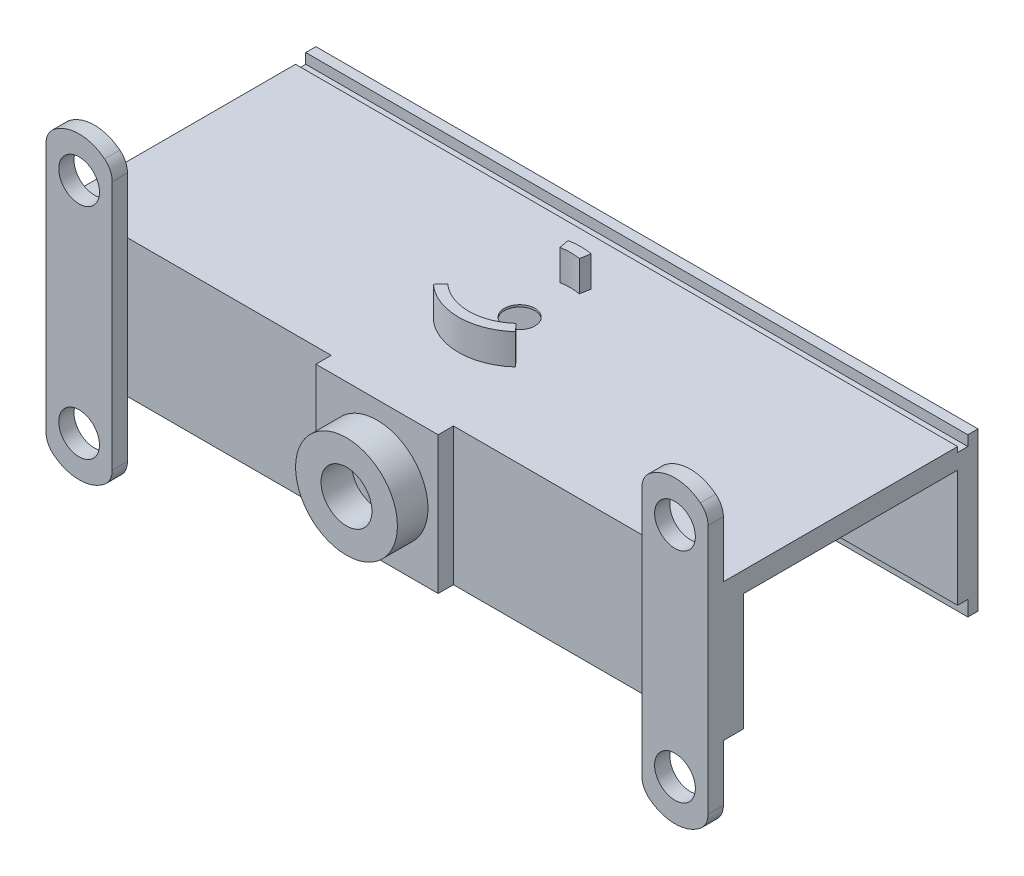
SolidWorks part; units mm, degrees
ref_plane "Alzado" through (0, 0, 0) normal (0, 0, 1) x (1, 0, 0)
ref_plane "Planta" through (0, 0, 0) normal (0, 1, 0) x (1, 0, 0)
ref_plane "Vista lateral" through (0, 0, 0) normal (1, 0, 0) x (0, 0, -1)
sketch "Croquis1" plane through (0, 0, 0) normal (0, 1, 0) x (1, 0, 0)
  line L0 (-32.5, 0) -> (32.5, 0)
  line L1 (32.5, 0) -> (32.5, -25)
  line L2 (32.5, -25) -> (-32.5, -25)
  line L3 (-32.5, -25) -> (-32.5, 0)
  dimension "D1" = 25
  dimension "D2" = 65
extrude "Saliente-Extruir4" add sketch "Croquis1" along normal blind 13.5
sketch "Croquis5" plane through (0, 0, 25) normal (0, 0, 1) x (1, 0, 0)
  line L0 (32.5, 0) -> (32.5, -5.5184)
  line L1 (-32.5, 13.5) -> (32.5, 13.5) construction
  line L2 (26, 13.5) -> (26, 0)
  line L3 (-32.5, 0) -> (32.5, 0) construction
  line L4 (26, 0) -> (26, -5.5184)
  line L5 (32.5, 0) -> (32.5, 13.5)
  line L6 (-32.5, 0) -> (-32.5, -5.5184)
  line L7 (26, 13.5) -> (26, 19.0184)
  line L8 (32.5, 13.5) -> (32.5, 19.0184)
  line L9 (-32.5, 6.75) -> (32.5, 6.75) construction
  line L10 (-32.5, 13.5) -> (-32.5, 0) construction
  line L11 (0, 19.3867) -> (0, -8.9745) construction
  line L12 (-26, 0) -> (-26, -5.5184)
  line L13 (-26, 13.5) -> (-26, 19.0184)
  line L14 (-32.5, 13.5) -> (-32.5, 19.0184)
  line L15 (-32.5, 0) -> (-32.5, 13.5)
  line L16 (-26, 13.5) -> (-26, 0)
  circle A0 centre (29.25, 17.4572) radius 2
  arc A1 (32.5, 19.0184) -> (31.75, 20.5797) centre (30.5, 19.0184) ccw
  arc A2 (26.75, 20.5797) -> (26, 19.0184) centre (28, 19.0184) ccw
  arc A3 (31.75, 20.5797) -> (26.75, 20.5797) centre (29.25, 17.4572) ccw
  arc A4 (32.5, -5.5184) -> (31.75, -7.0797) centre (30.5, -5.5184) cw
  arc A5 (31.75, -7.0797) -> (26.75, -7.0797) centre (29.25, -3.9572) cw
  arc A6 (26.75, -7.0797) -> (26, -5.5184) centre (28, -5.5184) cw
  circle A7 centre (29.25, -3.9572) radius 2
  arc A8 (-32.5, -5.5184) -> (-31.75, -7.0797) centre (-30.5, -5.5184) ccw
  arc A9 (-31.75, -7.0797) -> (-26.75, -7.0797) centre (-29.25, -3.9572) ccw
  arc A10 (-26.75, -7.0797) -> (-26, -5.5184) centre (-28, -5.5184) ccw
  arc A11 (-26.75, 20.5797) -> (-26, 19.0184) centre (-28, 19.0184) cw
  arc A12 (-31.75, 20.5797) -> (-26.75, 20.5797) centre (-29.25, 17.4572) cw
  arc A13 (-32.5, 19.0184) -> (-31.75, 20.5797) centre (-30.5, 19.0184) cw
  dimension "D2" = 4
  dimension "D3" = 2
  dimension "D1" = 6.5
sketch "Croquis6" plane through (32.5, 0, 0) normal (1, 0, 0) x (0, 0, -1)
  line L0 (-23, 0) -> (-23, 11.5)
  line L1 (-25, 0) -> (0, 0) construction
  line L2 (-23, 11.5) -> (-2, 11.5)
  line L3 (-2, 11.5) -> (-2, 0)
  line L4 (-2, 0) -> (-23, 0)
  line L5 (-25, 0) -> (-25, 13.5) construction
  line L6 (0, 13.5) -> (0, 0) construction
  line L7 (-25, 13.5) -> (0, 13.5) construction
  dimension "D1" = 2
  dimension "D2" = 2
  dimension "D3" = 2
extrude "Cortar-Extruir2" cut sketch "Croquis6" against normal blind 65
extrude "Saliente-Extruir6" add sketch "Croquis5" along normal blind 1.5
sketch "Croquis7" plane through (0, 0, 25) normal (0, 0, 1) x (1, 0, 0)
  line L0 (-26, -5.5184) -> (-26, 19.0184) construction
  line L1 (-26, 13.5) -> (26, 13.5) construction
  line L2 (-6, 13.5) -> (-6, 0)
  line L3 (-26, 0) -> (26, 0) construction
  line L4 (26, 13.5) -> (26, 0) construction
  line L5 (-6, 13.5) -> (6, 13.5)
  line L6 (6, 13.5) -> (6, 0)
  line L7 (-6, 0) -> (6, 0)
  dimension "D1" = 20
  dimension "D2" = 20
extrude "Saliente-Extruir7" add sketch "Croquis7" along normal blind 1.5
sketch "Croquis8" plane through (0, 0, 26.5) normal (0, 0, 1) x (1, 0, 0)
  line L0 (-6, 13.5) -> (6, 0) construction
  line L1 (-6, 0) -> (6, 13.5) construction
  circle A0 centre (0, 6.75) radius 5
  dimension "D1" = 10
extrude "Saliente-Extruir8" add sketch "Croquis8" along normal blind 3
sketch "Croquis9" plane through (0, 0, 29.5) normal (0, 0, 1) x (1, 0, 0)
  circle A0 centre (0, 6.75) radius 2.5
  dimension "D1" = 5
extrude "Cortar-Extruir3" cut sketch "Croquis9" against normal blind 3
sketch "Croquis10" plane through (0, 0, 0) normal (0, -1, 0) x (1, 0, 0)
  line L1 (-3, 25) -> (-3, 23)
  line L2 (-32.5, 23) -> (32.5, 23) construction
  line L3 (-3, 23) -> (3, 23)
  line L4 (3, 23) -> (3, 25)
  line L6 (-3, 25) -> (3, 25)
extrude "Cortar-Extruir4" cut sketch "Croquis10" against normal blind 10
sketch "Croquis11" plane through (0, 0, 26.5) normal (0, 0, 1) x (1, 0, 0)
  circle A0 centre (0, 6.75) radius 1.5
  dimension "D1" = 3
extrude "Cortar-Extruir5" cut sketch "Croquis11" against normal blind 10
sketch "Croquis12" plane through (0, 0, 26.5) normal (0, 0, 1) x (1, 0, 0)
  line L0 (-32.5, 6.75) -> (-26, 6.75) construction
  line L3 (-32.5, 19.0184) -> (-32.5, -5.5184) construction
  line L4 (-26, -5.5184) -> (-26, 19.0184) construction
  circle A0 centre (-29.25, 17.5) radius 2
  circle A1 centre (-29.25, -4) radius 2
  dimension "D2" = 4
extrude "Cortar-Extruir6" cut sketch "Croquis12" against normal blind 10
sketch "Croquis14" plane through (0, 0, 23) normal (0, 0, -1) x (-1, 0, 0)
  line L0 (-3, 10) -> (-3, 10.5)
  line L1 (32.5, 11.5) -> (-32.5, 11.5) construction
  line L2 (-2, 11.5) -> (2, 11.5)
  line L3 (3, 10.5) -> (3, 10)
  line L4 (3, 10) -> (-3, 10)
  arc A0 (-3, 10.5) -> (-2, 11.5) centre (-2, 10.5) cw
  arc A1 (2, 11.5) -> (3, 10.5) centre (2, 10.5) cw
  point P10 (-3, 11.5)
  point P13 (3, 11.5)
  dimension "D1" = 1
extrude "Cortar-Extruir7" cut sketch "Croquis14" against normal blind 2
sketch "Croquis15" plane through (0, 11.5, 0) normal (0, -1, 0) x (1, 0, 0)
  line L0 (-32.5, 12.5) -> (32.5, 12.5) construction
  line L1 (-32.5, 2) -> (-32.5, 23) construction
  line L2 (32.5, 2) -> (32.5, 23) construction
  line L3 (0, 36.9163) -> (0, -10.3528) construction
  circle A0 centre (0, 12.5) radius 1.5
  dimension "D1" = 3
extrude "Cortar-Extruir8" cut sketch "Croquis15" against normal blind 2
sketch "Croquis18" plane through (0, 11.5, 0) normal (0, -1, 0) x (1, 0, 0)
  circle A0 centre (0, 12.5) radius 6.5
  dimension "D1" = 13
extrude "Cortar-Extruir9" cut sketch "Croquis18" against normal blind 1.8
sketch "Croquis19" plane through (0, 13.5, 0) normal (0, 1, 0) x (1, 0, 0)
  line L0 (-3.3595, -16.2032) -> (-4.0314, -16.9438)
  line L1 (3.3595, -16.2032) -> (4.0314, -16.9438)
  line L2 (-1.133, -6.6079) -> (-0.9441, -7.5899)
  line L4 (1.133, -6.6079) -> (0.9441, -7.5899)
  arc A0 (-3.3595, -16.2032) -> (3.3595, -16.2032) centre (0, -12.5) ccw
  arc A1 (-4.0314, -16.9438) -> (4.0314, -16.9438) centre (0, -12.5) ccw
  arc A2 (1.133, -6.6079) -> (-1.133, -6.6079) centre (0, -12.5) ccw
  arc A3 (0.9441, -7.5899) -> (-0.9441, -7.5899) centre (0, -12.5) ccw
  dimension "D1" = 10
  dimension "D2" = 12
extrude "Saliente-Extruir9" add sketch "Croquis19" along normal blind 3
sketch "Croquis20" plane through (0, 0, 0) normal (0, -1, 0) x (1, 0, 0)
  line L0 (-32.5, 1) -> (32.5, 1)
  line L1 (-32.5, 0) -> (-32.5, 2) construction
  line L2 (32.5, 2) -> (32.5, 0) construction
  line L3 (32.5, 1) -> (32.5, 0)
  line L4 (32.5, 0) -> (-32.5, 0)
  line L5 (-32.5, 0) -> (-32.5, 1)
extrude "Saliente-Extruir10" add sketch "Croquis20" along normal blind 1.5
sketch "Croquis21" plane through (0, 13.5, 0) normal (0, 1, 0) x (1, 0, 0)
  line L0 (-32.5, 0) -> (32.5, 0)
  line L1 (32.5, 0) -> (32.5, -1)
  line L2 (32.5, -25) -> (32.5, 0) construction
  line L3 (32.5, -1) -> (-32.5, -1)
  line L4 (-32.5, 0) -> (-32.5, -25) construction
  line L5 (-32.5, -1) -> (-32.5, 0)
  dimension "D1" = 1
extrude "Saliente-Extruir11" add sketch "Croquis21" along normal blind 0.5
sketch "Croquis22" plane through (0, 13.5, 0) normal (0, 1, 0) x (1, 0, 0)
  line L0 (-32.5, -1) -> (32.5, -1)
  line L1 (32.5, -1) -> (32.5, -2)
  line L2 (32.5, -25) -> (32.5, -1) construction
  line L3 (32.5, -2) -> (-32.5, -2)
  line L4 (-32.5, -1) -> (-32.5, -25) construction
  line L5 (-32.5, -2) -> (-32.5, -1)
  dimension "D1" = 1
extrude "Cortar-Extruir10" cut sketch "Croquis22" against normal blind 0.5
